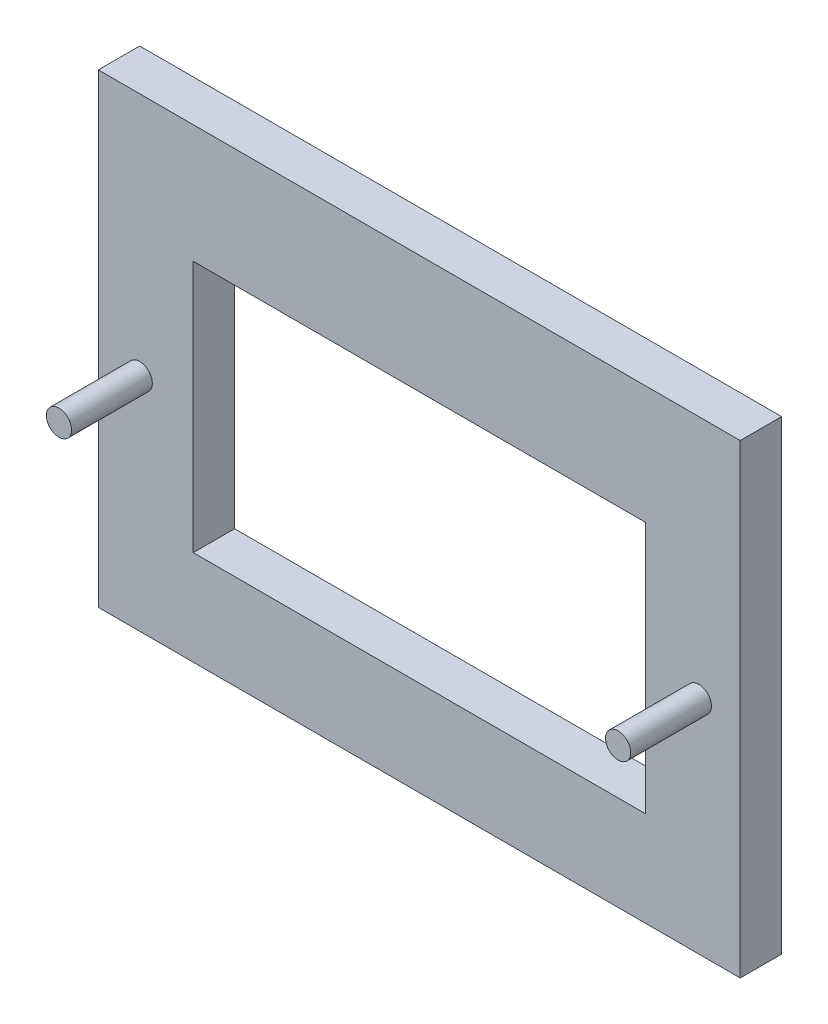
SolidWorks part; units mm, degrees
ref_plane "Front Plane" through (0, 0, 0) normal (0, 0, 1) x (1, 0, 0)
ref_plane "Top Plane" through (0, 0, 0) normal (0, 1, 0) x (1, 0, 0)
ref_plane "Right Plane" through (0, 0, 0) normal (1, 0, 0) x (0, 0, -1)
sketch "Sketch1" plane through (0, 0, 0) normal (0, 0, 1) x (1, 0, 0)
  line L0 (15.9, 0) -> (15.9, 4.7)
  line L1 (0, 0) -> (31.8, 0)
  line L2 (0, 0) -> (0, 21.9)
  line L4 (31.8, 0) -> (31.8, 21.9)
  line L5 (31.8, 10.95) -> (27.1, 10.95)
  line L6 (0, 10.95) -> (4.7, 10.95)
  line L7 (15.9, 21.9) -> (15.9, 17.2)
  line L8 (0, 10.95) -> (2.05, 10.95)
  line L9 (27.1, 4.7) -> (4.7, 4.7)
  line L10 (27.1, 4.7) -> (27.1, 17.2)
  line L11 (27.1, 17.2) -> (4.7, 17.2)
  line L12 (4.7, 4.7) -> (4.7, 17.2)
  line L13 (31.8, 10.95) -> (29.75, 10.95)
  line L14 (15.9, 21.9) -> (15.9, 23.06)
  line L15 (0, 21.9) -> (0, 23.06)
  line L16 (31.8, 21.9) -> (31.8, 23.06)
  line L17 (31.8, 23.06) -> (0, 23.06)
  circle A0 centre (29.75, 10.95) radius 0.625
  circle A1 centre (2.05, 10.95) radius 0.625
  dimension "D9" = 1.25
  dimension "D10" = 1.25
  dimension "D1" = 31.8
  dimension "D2" = 21.9
  dimension "D3" = 4.7
  dimension "D4" = 4.7
  dimension "D5" = 4.7
  dimension "D6" = 4.7
  dimension "D7" = 2.05
  dimension "D8" = 2.05
  dimension "D11" = 1.16
  dimension "D12" = 1.16
extrude "Boss-Extrude1" add sketch "Sketch1" along normal blind 2.05
sketch "Sketch4" plane through (0, 0, 2.05) normal (0, 0, 1) x (1, 0, 0)
  circle A0 centre (2.05, 10.95) radius 0.625
  circle A1 centre (29.75, 10.95) radius 0.625
extrude "Boss-Extrude2" add sketch "Sketch4" along normal blind 4 separate body
sketch "Sketch6" plane through (0, 0, 2.05) normal (0, 0, 1) x (1, 0, 0)
  line L0 (27.1, 10.95) -> (20.85, 10.95) construction
  line L1 (27.1, 4.7) -> (27.1, 17.2) construction
  line L2 (20.85, 10.95) -> (20.85, 18.92) construction
  line L3 (20.85, 18.92) -> (20.85, 26.89) construction
  circle A0 centre (20.85, 10.95) radius 6.25
  circle A1 centre (20.85, 10.95) radius 3.1
  circle A2 centre (20.85, 18.92) radius 3.1
  circle A3 centre (20.85, 26.89) radius 3.1
  dimension "D2" = 12.5
  dimension "D3" = 6.2
  dimension "D5" = 6.2
  dimension "D7" = 6.2
  dimension "D1" = 6.25
  dimension "D4" = 7.97
  dimension "D6" = 7.97
